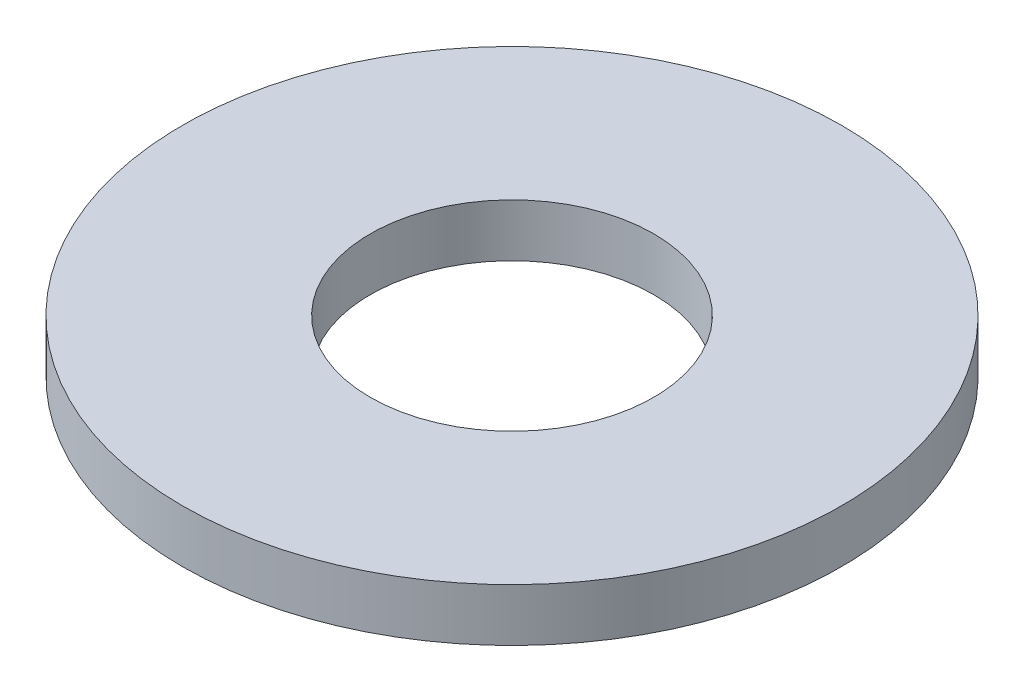
SolidWorks part; units mm, degrees
ref_plane "Front Plane" through (0, 0, 0) normal (0, 0, 1) x (1, 0, 0)
ref_plane "Top Plane" through (0, 0, 0) normal (0, 1, 0) x (1, 0, 0)
ref_plane "Right Plane" through (0, 0, 0) normal (1, 0, 0) x (0, 0, -1)
sketch "Sketch2" plane through (0, 0, 0) normal (0, 1, 0) x (1, 0, 0)
  circle A0 centre (0, 0) radius 5
  circle A1 centre (0, 0) radius 2.15
  dimension "D1" = 4.3
  dimension "D2" = 10
extrude "Boss-Extrude1" add sketch "Sketch2" along normal blind 0.8
